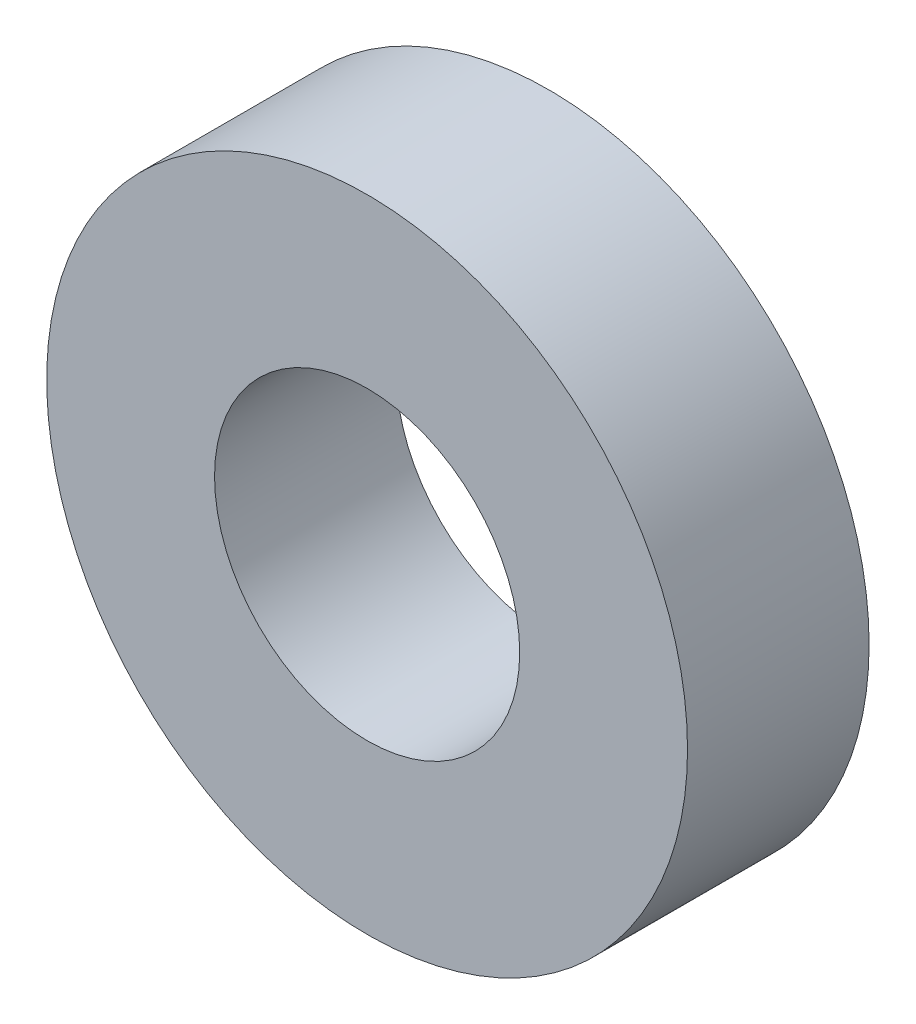
SolidWorks part; units mm, degrees
ref_plane "Alzado" through (0, 0, 0) normal (0, 0, 1) x (1, 0, 0)
ref_plane "Planta" through (0, 0, 0) normal (0, 1, 0) x (1, 0, 0)
ref_plane "Vista lateral" through (0, 0, 0) normal (1, 0, 0) x (0, 0, -1)
sketch "Croquis1" plane through (0, 0, 0) normal (0, 0, 1) x (1, 0, 0)
  circle A0 centre (0, 0) radius 10
  circle A1 centre (0, 0) radius 21
  dimension "D1" = 42
  dimension "D2" = 20
extrude "Saliente-Extruir1" add sketch "Croquis1" along normal blind 11.9
